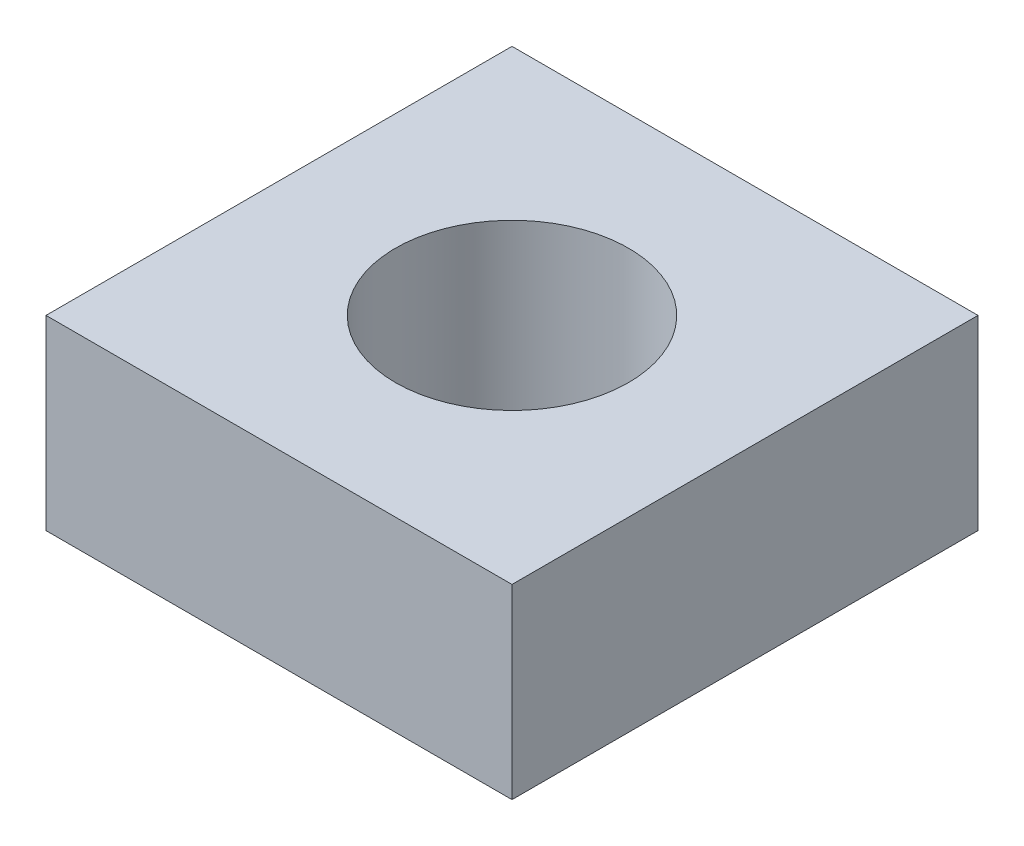
SolidWorks part; units mm, degrees
ref_plane "Front Plane" through (0, 0, 0) normal (0, 0, 1) x (1, 0, 0)
ref_plane "Top Plane" through (0, 0, 0) normal (0, 1, 0) x (1, 0, 0)
ref_plane "Right Plane" through (0, 0, 0) normal (1, 0, 0) x (0, 0, -1)
sketch "Sketch1" plane through (0, 0, 0) normal (0, 1, 0) x (1, 0, 0)
  line L1 (-25, -25) -> (25, -25)
  line L2 (-25, -25) -> (-25, 25)
  line L3 (-25, 25) -> (25, 25)
  line L4 (25, -25) -> (25, 25)
  line L5 (-25, -25) -> (25, 25) construction
  line L6 (-25, 25) -> (25, -25) construction
  circle A0 centre (0, 0) radius 12.5
  point P0 (0, 0)
  dimension "D3" = 25
  dimension "D1" = 50
  dimension "D2" = 50
extrude "Boss-Extrude1" add sketch "Sketch1" along normal blind 20
